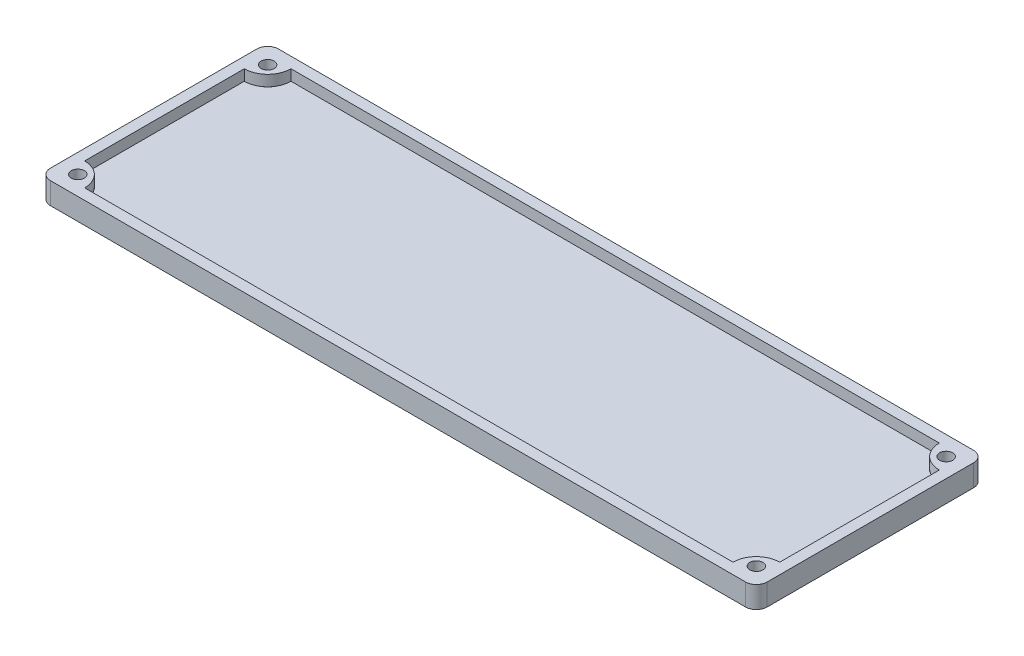
SolidWorks part; units mm, degrees
material "ABS"
ref_plane "Alzado" through (0, 0, 0) normal (0, 0, 1) x (1, 0, 0)
ref_plane "Planta" through (0, 0, 0) normal (0, 1, 0) x (1, 0, 0)
ref_plane "Vista lateral" through (0, 0, 0) normal (1, 0, 0) x (0, 0, -1)
sketch "Croquis1" plane through (0, 0, 0) normal (0, 1, 0) x (1, 0, 0)
  line L1 (0, 0) -> (66.01, 0)
  line L2 (0, 0) -> (0, 21)
  line L3 (0, 21) -> (66.01, 21)
  line L4 (66.01, 0) -> (66.01, 21)
  dimension "D1" = 66.01
  dimension "D2" = 21
extrude "Saliente-Extruir1" add sketch "Croquis1" along normal blind 1
ref_plane "Plano1" through (0, 1, 0) normal (0, 1, 0) x (1, 0, 0)
sketch "Croquis2" plane through (0, 1, 0) normal (0, 1, 0) x (1, 0, 0)
  line L0 (66.01, 0) -> (66.01, 21) construction
  line L1 (0, 0) -> (66.01, 0) construction
  line L2 (0, 21) -> (0, 0) construction
  line L3 (66.01, 21) -> (0, 21) construction
  line L4 (66.01, 0) -> (66.01, 21)
  line L5 (0, 0) -> (66.01, 0)
  line L6 (0, 21) -> (0, 0)
  line L7 (66.01, 21) -> (0, 21)
  line L9 (1, 20) -> (65.01, 20)
  line L10 (1, 20) -> (1, 1)
  line L11 (1, 1) -> (65.01, 1)
  line L12 (65.01, 20) -> (65.01, 1)
  dimension "D1" = 1
  dimension "D2" = 1
  dimension "D3" = 1
  dimension "D4" = 1
extrude "Saliente-Extruir2" add sketch "Croquis2" along normal blind 1
ref_plane "Plano2" through (0, 2, 0) normal (0, 1, 0) x (1, 0, 0)
sketch "Croquis4" plane through (0, 2, 0) normal (0, 1, 0) x (1, 0, 0)
  line L0 (1, 20) -> (1, 17.85)
  line L1 (1, 20) -> (1, 1) construction
  line L2 (1, 20) -> (3.15, 20)
  line L3 (65.01, 20) -> (1, 20) construction
  line L5 (1, 1) -> (1, 3.15)
  line L6 (1, 1) -> (3.15, 1)
  line L7 (1, 1) -> (65.01, 1) construction
  line L9 (65.01, 20) -> (62.86, 20)
  line L10 (65.01, 20) -> (65.01, 17.85)
  line L11 (65.01, 1) -> (65.01, 20) construction
  line L13 (65.01, 1) -> (62.86, 1)
  line L14 (65.01, 1) -> (65.01, 3.15)
  line L15 (65.01, 1) -> (65.01, 20) construction
  line L19 (1, 20) -> (2.5203, 18.4797) construction
  line L20 (1, 1) -> (2.5203, 2.5203) construction
  line L21 (65.01, 1) -> (63.4897, 2.5203) construction
  line L22 (65.01, 20) -> (63.4897, 18.4797) construction
  arc A11 (3.15, 20) -> (1, 17.85) centre (1, 20) cw
  arc A12 (1, 3.15) -> (3.15, 1) centre (1, 1) cw
  arc A13 (65.01, 3.15) -> (62.86, 1) centre (65.01, 1) ccw
  arc A14 (62.86, 20) -> (65.01, 17.85) centre (65.01, 20) ccw
  dimension "D1" = 2.15
  dimension "D2" = 2.15
  dimension "D4" = 2.15
  dimension "D5" = 2.15
  dimension "D7" = 2.15
  dimension "D8" = 2.15
  dimension "D10" = 2.15
  dimension "D11" = 2.15
extrude "Saliente-Extruir3" add sketch "Croquis4" against normal up to next
sketch "Croquis5" plane through (0, 2, 0) normal (0, 1, 0) x (1, 0, 0)
  line L6 (1, 20) -> (2.5203, 18.4797) construction
  line L7 (1, 1) -> (2.5203, 2.5203) construction
  line L8 (65.01, 20) -> (63.4897, 18.4797) construction
  line L9 (65.01, 1) -> (63.4897, 2.5203) construction
  circle A6 centre (1.7601, 19.2399) radius 0.6
  circle A7 centre (1.7601, 1.7601) radius 0.6
  circle A8 centre (64.2499, 19.2399) radius 0.6
  circle A9 centre (64.2499, 1.7601) radius 0.6
  dimension "D1" = 1.2
  dimension "D2" = 1.2
  dimension "D3" = 1.2
  dimension "D4" = 1.2
extrude "Cortar-Extruir1" cut sketch "Croquis5" against normal through all
ref_plane "Plano3" through (0, 0, 0) normal (0, -1, 0) x (-1, 0, 0)
sketch "Croquis6" plane through (0, 0, 0) normal (0, -1, 0) x (-1, 0, 0)
  circle A4 centre (-64.2499, 1.7601) radius 1.1
  circle A5 centre (-64.2499, 19.2399) radius 1.1
  circle A6 centre (-1.7601, 19.2399) radius 1.1
  circle A7 centre (-1.7601, 1.7601) radius 1.1
  point P3 (-1.7601, 17.2399)
  point P4 (-1.7601, 1.7601)
  dimension "D1" = 2.2
  dimension "D2" = 2.2
  dimension "D3" = 2.2
  dimension "D4" = 2.2
extrude "Cortar-Extruir2" cut sketch "Croquis6" against normal blind 1
fillet "Redondeo1" radius 1 4 edges at (66.01, 1, 0) (66.01, 1, -21) (0, 1, 0) (0, 1, -21)
